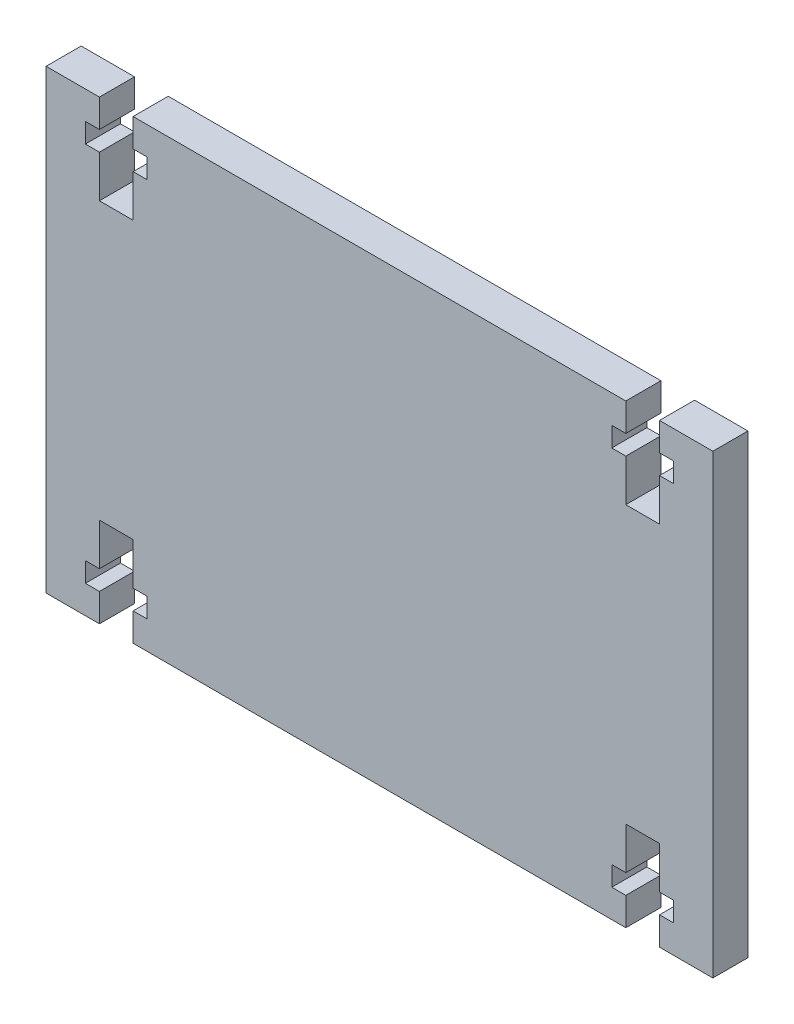
SolidWorks part; units mm, degrees
ref_plane "Front Plane" through (0, 0, 0) normal (0, 0, 1) x (1, 0, 0)
ref_plane "Top Plane" through (0, 0, 0) normal (0, 1, 0) x (1, 0, 0)
ref_plane "Right Plane" through (0, 0, 0) normal (1, 0, 0) x (0, 0, -1)
sketch "Sketch1" plane through (0, 0, 0) normal (0, 0, 1) x (1, 0, 0)
  line L0 (0, 32.5) -> (0, 35.5344) construction
  line L1 (-47.5, 32.5) -> (-39.9, 32.5)
  line L2 (-47.5, 32.5) -> (-47.5, -32.5)
  line L3 (-47.5, -32.5) -> (-39.9, -32.5)
  line L4 (47.5, 32.5) -> (47.5, -32.5)
  line L5 (-47.5, 32.5) -> (47.5, -32.5) construction
  line L6 (-47.5, -32.5) -> (47.5, 32.5) construction
  line L7 (-37.5, 32.5) -> (-37.5, 17.7658) construction
  line L8 (-35.1, 32.5) -> (-35.1, 28.5)
  line L9 (-35.1, 28.5) -> (-33.1, 28.5)
  line L10 (-33.1, 28.5) -> (-33.1, 25.7)
  line L11 (-33.1, 25.7) -> (-35.1, 25.7)
  line L12 (-35.1, 25.7) -> (-35.1, 19.7)
  line L13 (-39.9, 25.7) -> (-39.9, 19.7)
  line L14 (-41.9, 25.7) -> (-39.9, 25.7)
  line L15 (-41.9, 28.5) -> (-41.9, 25.7)
  line L16 (-39.9, 28.5) -> (-41.9, 28.5)
  line L17 (-39.9, 32.5) -> (-39.9, 28.5)
  line L18 (-39.9, 19.7) -> (-35.1, 19.7)
  line L19 (0, 0) -> (15.1344, 0) construction
  line L20 (39.9, 19.7) -> (35.1, 19.7)
  line L21 (39.9, 25.7) -> (39.9, 19.7)
  line L22 (35.1, 25.7) -> (35.1, 19.7)
  line L23 (33.1, 25.7) -> (35.1, 25.7)
  line L24 (33.1, 28.5) -> (33.1, 25.7)
  line L25 (35.1, 28.5) -> (33.1, 28.5)
  line L26 (35.1, 32.5) -> (35.1, 28.5)
  line L27 (39.9, 32.5) -> (39.9, 28.5)
  line L28 (39.9, 28.5) -> (41.9, 28.5)
  line L29 (41.9, 25.7) -> (39.9, 25.7)
  line L30 (41.9, 28.5) -> (41.9, 25.7)
  line L31 (41.9, -28.5) -> (41.9, -25.7)
  line L32 (41.9, -25.7) -> (39.9, -25.7)
  line L33 (39.9, -28.5) -> (41.9, -28.5)
  line L34 (39.9, -32.5) -> (39.9, -28.5)
  line L35 (35.1, -32.5) -> (35.1, -28.5)
  line L36 (35.1, -28.5) -> (33.1, -28.5)
  line L37 (33.1, -28.5) -> (33.1, -25.7)
  line L38 (33.1, -25.7) -> (35.1, -25.7)
  line L39 (35.1, -25.7) -> (35.1, -19.7)
  line L40 (39.9, -25.7) -> (39.9, -19.7)
  line L41 (39.9, -19.7) -> (35.1, -19.7)
  line L42 (-37.5, -32.5) -> (-37.5, -17.7658) construction
  line L43 (-39.9, -19.7) -> (-35.1, -19.7)
  line L44 (-39.9, -32.5) -> (-39.9, -28.5)
  line L45 (-39.9, -28.5) -> (-41.9, -28.5)
  line L46 (-41.9, -28.5) -> (-41.9, -25.7)
  line L47 (-41.9, -25.7) -> (-39.9, -25.7)
  line L48 (-39.9, -25.7) -> (-39.9, -19.7)
  line L49 (-35.1, -25.7) -> (-35.1, -19.7)
  line L50 (-33.1, -25.7) -> (-35.1, -25.7)
  line L51 (-33.1, -28.5) -> (-33.1, -25.7)
  line L52 (-35.1, -28.5) -> (-33.1, -28.5)
  line L53 (-35.1, -32.5) -> (-35.1, -28.5)
  line L54 (39.9, 32.5) -> (47.5, 32.5)
  line L55 (39.9, -32.5) -> (47.5, -32.5)
  line L56 (-35.1, 32.5) -> (35.1, 32.5)
  line L57 (-35.1, -32.5) -> (35.1, -32.5)
  point P0 (0, 0)
  dimension "D1" = 95
  dimension "D2" = 65
  dimension "D3" = 10
  dimension "D4" = 4
  dimension "D5" = 2.8
  dimension "D6" = 2.4
  dimension "D7" = 2.4
  dimension "D8" = 2
  dimension "D9" = 6
extrude "Boss-Extrude1" add sketch "Sketch1" along normal blind 5
